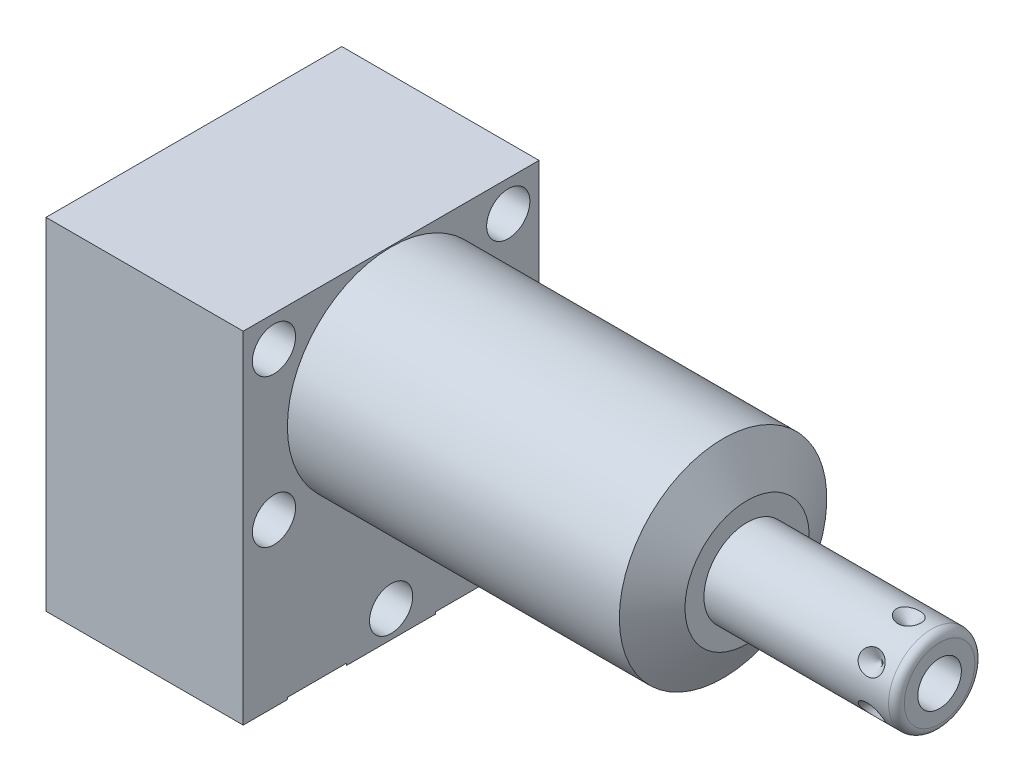
SolidWorks part; units mm, degrees
material "Alloy Steel"
ref_plane "Front Plane" through (0, 0, 0) normal (0, 0, 1) x (1, 0, 0)
ref_plane "Top Plane" through (0, 0, 0) normal (0, 1, 0) x (1, 0, 0)
ref_plane "Right Plane" through (0, 0, 0) normal (1, 0, 0) x (0, 0, -1)
ref_plane "Plane1" through (0, 0, 0) normal (1, 0, 0) x (0, 0, -1)
sketch "Sketch1" plane through (0, 0, 0) normal (1, 0, 0) x (0, 0, -1)
  line L0 (-19.05, 13.4874) -> (-19.05, -30.4546)
  line L1 (-19.05, -30.4546) -> (19.05, -30.4546)
  line L2 (19.05, -30.4546) -> (19.05, 13.4874)
  line L3 (19.05, 13.4874) -> (-19.05, 13.4874)
  line L4 (0, -32.6517) -> (0, 15.6845) construction
  dimension "D1" = 38.1
  dimension "D2" = 43.942
  dimension "D3" = 13.4874
extrude "Extrude1" add sketch "Sketch1" along normal blind 45.847 and the other way blind 25.4
ref_plane "Plane2" through (0, 0, 0) normal (1, 0, 0) x (0, 0, -1)
sketch "Sketch2" plane through (0, 0, 0) normal (1, 0, 0) x (0, 0, -1)
  line L0 (-14.6964, 0) -> (14.6964, 0) construction
  line L5 (19.05, 13.4874) -> (-19.05, 13.4874)
  line L6 (-19.05, 13.4874) -> (-19.05, -30.4546)
  line L7 (-19.05, -30.4546) -> (19.05, -30.4546)
  line L8 (19.05, -30.4546) -> (19.05, 13.4874)
  line L9 (19.05, 13.4874) -> (-19.05, 13.4874)
  line L10 (-19.05, 13.4874) -> (-19.05, -30.4546)
  line L11 (-19.05, -30.4546) -> (19.05, -30.4546)
  line L12 (19.05, -30.4546) -> (19.05, 13.4874)
  circle A0 centre (0, 0) radius 13.3604
  dimension "D1" = 26.7208
  dimension "D2" = 0
extrude "Cut-Extrude1" cut sketch "Sketch2" along normal up to next
ref_plane "Plane3" through (0, 0, 0) normal (0, 0, 1) x (1, 0, 0)
sketch "Sketch3" plane through (0, 0, 0) normal (0, 0, 1) x (1, 0, 0)
  line L0 (42.7527, 13.3604) -> (45.847, 8.001)
  line L1 (42.598, 0) -> (46.0017, 0) construction
  line L2 (45.847, 13.3604) -> (45.847, 8.001)
  line L3 (45.847, 13.3604) -> (42.7527, 13.3604)
  line L4 (45.847, 13.3604) -> (0, 13.3604) construction
  line L5 (45.847, -13.3604) -> (45.847, 13.3604) construction
  dimension "D1" = 30
  dimension "D2" = 16.002
revolve "Cut-Revolve1" cut sketch "Sketch3" angle 360 about L1
ref_plane "Plane4" through (-22.733, -19.8374, 9.525) normal (0, 0, 1) x (0, 1, 0)
sketch "S2D0002" plane through (-22.733, -19.8374, 9.525) normal (0, 0, 1) x (0, 1, 0)
  line L0 (-0.8128, 0) -> (3.7338, 0)
  line L1 (3.7338, 0) -> (3.2938, -2.0701)
  line L2 (3.2938, -2.0701) -> (2.6416, -2.7223)
  line L3 (2.6416, -2.7223) -> (2.6416, -13.97)
  line L4 (2.6416, -13.97) -> (-0.8128, -13.97)
  line L5 (-0.8128, -13.97) -> (-0.8128, 0)
  line L6 (-0.8128, -14.6685) -> (-0.8128, 0.6985) construction
  line L7 (19.8374, -65.4857) -> (19.8374, -22.733) construction
  dimension "D1" = 13.97
  dimension "D2" = 20.6502
revolve "Cut-Revolve2" cut sketch "S2D0002" angle 360 about L6
ref_plane "Plane5" through (-22.733, -19.8374, -9.525) normal (0, 0, 1) x (0, 1, 0)
sketch "Sketch5" plane through (-22.733, -19.8374, -9.525) normal (0, 0, 1) x (0, 1, 0)
  line L0 (-0.8128, 0) -> (3.7338, 0)
  line L1 (3.7338, 0) -> (3.2938, -2.0701)
  line L2 (3.2938, -2.0701) -> (2.6416, -2.7223)
  line L3 (2.6416, -2.7223) -> (2.6416, -13.97)
  line L4 (2.6416, -13.97) -> (-0.8128, -13.97)
  line L5 (-0.8128, -13.97) -> (-0.8128, 0)
  line L6 (-0.8128, -14.6685) -> (-0.8128, 0.6985) construction
  line L7 (19.8374, -65.4857) -> (19.8374, -22.733) construction
  dimension "D1" = 13.97
  dimension "D2" = 20.6502
revolve "Cut-Revolve3" cut sketch "Sketch5" angle 360 about L6
ref_plane "Plane6" through (-8.7376, -30.2006, 9.525) normal (0, 0, 1) x (-1, 0, 0)
sketch "Sketch14" plane through (-25.4, 0, 0) normal (-1, 0, 0) x (0, 0, 1)
  circle A0 centre (-9.525, -20.6502) radius 7.9375
  circle A1 centre (9.525, -20.6502) radius 7.9375
  dimension "D1" = 15.875
extrude "Cut-Extrude2" cut sketch "Sketch14" against normal blind 2.667
sketch "Sketch6" plane through (-8.7376, -30.2006, 9.525) normal (0, 0, 1) x (-1, 0, 0)
  line L0 (16.6624, -43.688) -> (16.6624, 0.254) construction
  line L1 (6.1836, 0) -> (5.641, -2.5527)
  line L2 (5.641, -2.5527) -> (4.9771, -3.2166)
  line L3 (4.9771, -3.2166) -> (4.9771, -17.272)
  line L4 (4.9771, -17.272) -> (0, -17.272)
  line L5 (0, -17.272) -> (0, 0)
  line L6 (0, -18.1356) -> (0, 0.8636) construction
  line L7 (6.1836, 0) -> (9.5237, 0)
  line L8 (9.5237, 0) -> (9.5237, 0.254)
  line L9 (16.6624, 0.254) -> (-8.7376, 0.254) construction
  line L10 (9.5237, 0.254) -> (0, 0.254)
  line L11 (0, 0.254) -> (0, 0)
  dimension "D1" = 19.0475
  dimension "D2" = 0.254
  dimension "D3" = 16.6624
revolve "Cut-Revolve4" cut sketch "Sketch6" angle 360 about L6
ref_plane "Plane7" through (-8.7376, -30.2006, -9.525) normal (0, 0, 1) x (-1, 0, 0)
sketch "Sketch7" plane through (-8.7376, -30.2006, -9.525) normal (0, 0, 1) x (-1, 0, 0)
  line L0 (16.6624, -43.688) -> (16.6624, 0.254) construction
  line L1 (6.1849, 0) -> (5.6423, -2.5527)
  line L2 (5.6423, -2.5527) -> (4.9784, -3.2166)
  line L3 (4.9784, -3.2166) -> (4.9784, -17.272)
  line L4 (4.9784, -17.272) -> (0, -17.272)
  line L5 (0, -17.272) -> (0, 0)
  line L6 (0, -18.1356) -> (0, 0.8636) construction
  line L7 (6.1849, 0) -> (9.5237, 0)
  line L8 (9.5237, 0) -> (-8.7376, 0) construction
  line L9 (9.5237, 0) -> (9.5237, 0.254)
  line L10 (16.6624, 0.254) -> (-8.7376, 0.254) construction
  line L11 (9.5237, 0.254) -> (0, 0.254)
  line L12 (0, 0.254) -> (0, 0)
  dimension "D1" = 16.6624
  dimension "D2" = 9.9568
  dimension "D3" = 19.0475
revolve "Cut-Revolve5" cut sketch "Sketch7" angle 360 about L6
ref_plane "Plane8" through (0, 0, 0) normal (0, 0, 1) x (1, 0, 0)
sketch "Sketch8" plane through (0, 0, 0) normal (0, 0, 1) x (1, 0, 0)
  line L0 (45.847, 0) -> (45.847, 5.5562)
  line L1 (45.847, 5.5562) -> (69.6214, 5.5562)
  line L2 (70.6374, 4.5403) -> (70.6374, 0)
  line L3 (70.6374, 0) -> (45.847, 0)
  line L4 (44.8323, 0) -> (67.1563, 0) construction
  line L5 (45.847, -8.001) -> (45.847, 8.001) construction
  line L6 (-25.4, 13.4874) -> (-25.4, -30.4546) construction
  arc A0 (70.6374, 4.5403) -> (69.6214, 5.5562) centre (69.6214, 4.5403) ccw
  point P0 (45.847, 0)
  dimension "D3" = 1.016
  dimension "D1" = 96.0374
  dimension "D2" = 11.1125
revolve "Revolve1" add sketch "Sketch8" angle 360 about L4
ref_plane "Plane9" through (66.1416, -2.8067, 0) normal (0, 0, 1) x (0, -1, 0)
sketch "S2D0001" plane through (66.1416, -2.8067, 0) normal (0, 0, 1) x (0, -1, 0)
  line L0 (0, 4.4958) -> (0, -5.6642)
  line L1 (0, -5.6642) -> (-2.8067, -7.3506)
  line L2 (0, 4.4958) -> (-2.8067, 4.4958)
  line L3 (-2.8067, 4.4958) -> (-2.8067, -7.3506)
  line L4 (-2.8067, -12.4388) -> (-2.8067, 0.5923) construction
  line L5 (1.7335, 4.4958) -> (-7.3469, 4.4958) construction
  dimension "D1" = 5.6134
  dimension "D2" = 10.16
  dimension "D3" = 59
revolve "Cut-Revolve6" cut sketch "S2D0001" angle 360 about L4
ref_plane "Plane12" through (62.1792, -5.5562, 0) normal (0, 0, 1) x (-1, 0, 0)
sketch "Sketch12" plane through (62.1792, -5.5562, 0) normal (0, 0, 1) x (-1, 0, 0)
  line L0 (-4.4958, 0) -> (-2.9083, 0)
  line L1 (-2.9083, 0) -> (-4.4958, -1.5875)
  line L2 (-4.4958, 0) -> (-4.4958, -1.5875)
  line L3 (-4.4958, -3.434) -> (-4.4958, 0.0794) construction
  line L4 (16.3322, 0) -> (-7.4422, 0) construction
  line L5 (-8.4582, -1.016) -> (-8.4582, -10.0965) construction
  dimension "D1" = 3.9624
  dimension "D2" = 45
  dimension "D3" = 3.175
revolve "Cut-Revolve7" cut sketch "Sketch12" angle 360 about L3
pattern_circular "CirPattern1" count 6 over 360 about axis through (45.848, 0, 0) along (-1, 0, 0) of "Cut-Revolve7"
hole_wizard "Hole1" positions "Sketch17" profile "Sketch16" legacy end condition up to next
sketch "Sketch17" plane through (0, 0, 0) normal (1, 0, 0) x (0, 0, -1)
  line L0 (0, 0) -> (0, 17.9298) construction
  line L1 (0, 0) -> (-24.6425, 0) construction
  point P0 (-15.0876, 9.525)
  point P10 (-15.0876, -9.525)
  point P12 (15.0876, 9.525)
  point P13 (15.0876, -9.525)
  point P14 (0, -26.9748)
  dimension "D1" = 9.525
  dimension "D2" = 15.0876
  dimension "D3" = 26.9748
sketch "Sketch16" plane through (0, 9.525, 15.0876) normal (0, 1, 0) x (0, 0, -1)
  line L0 (0, 0) -> (0, 25.4)
  line L1 (0, 25.4) -> (2.7813, 25.4)
  line L2 (2.7813, 25.4) -> (2.7813, 0)
  line L3 (2.7813, 0) -> (0, 0)
  line L4 (0, 110) -> (0, -10) construction
  dimension "Diameter" = 5.5626
  dimension "Depth" = 25.4
sketch "Sketch18" plane through (-8.7376, -30.2006, 9.525) normal (0, 0, 1) x (-1, 0, 0)
  line L0 (-0.6385, -9.5504) -> (23.3703, -9.5504) construction
  line L1 (11.2731, -9.5504) -> (3.5849, -9.5504) construction
  line L3 (13.9954, -17.4879) -> (13.9954, -1.6129) construction
  circle A0 centre (15.7607, -3.3782) radius 1.7653
  dimension "D1" = 3.5306
  dimension "D2" = 12.3444
revolve "Revolve2" add sketch "Sketch18" angle 360 about L0
